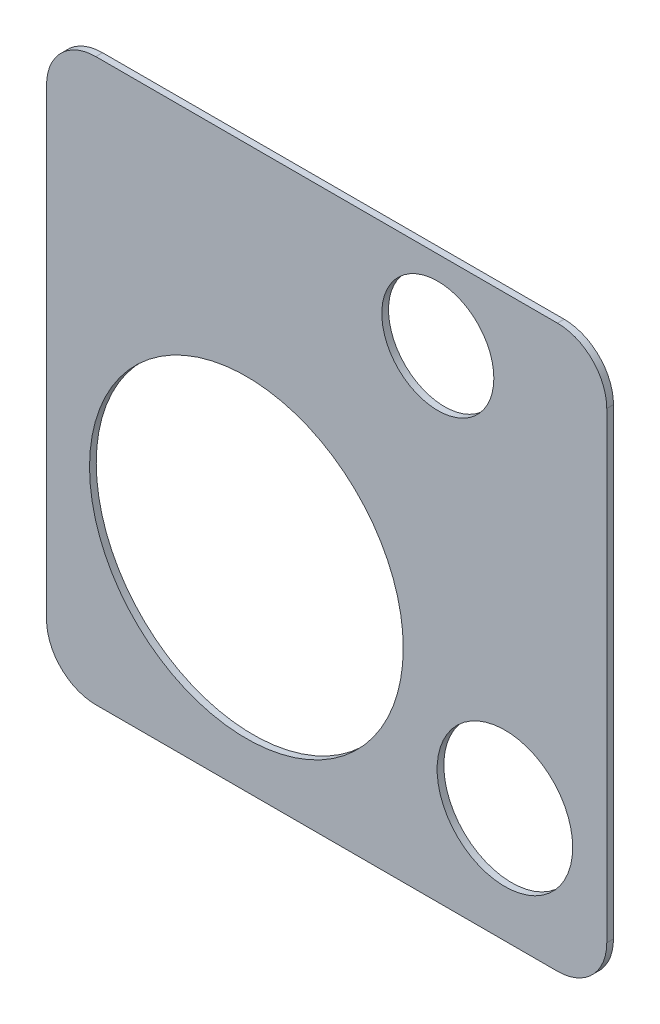
SolidWorks part; units mm, degrees
material "Pine"
ref_plane "Front Plane" through (0, 0, 0) normal (0, 0, 1) x (1, 0, 0)
ref_plane "Top Plane" through (0, 0, 0) normal (0, 1, 0) x (1, 0, 0)
ref_plane "Right Plane" through (0, 0, 0) normal (1, 0, 0) x (0, 0, -1)
sketch "Sketch1" plane through (0, 0, 0) normal (0, 0, 1) x (1, 0, 0)
  line L1 (0, 0) -> (500, 0)
  line L2 (0, 0) -> (0, 501)
  line L3 (0, 501) -> (500, 501)
  line L4 (500, 0) -> (500, 501)
  dimension "D1" = 500
  dimension "D2" = 501
extrude "Boss-Extrude1" add sketch "Sketch1" along normal blind 6
fillet "Fillet1" radius 44 4 edges at (0, 0, 3) (500, 0, 3) (0, 501, 3) (500, 501, 3)
sketch "Sketch2" plane through (0, 0, 6) normal (0, 0, 1) x (1, 0, 0)
  circle A0 centre (178.369, 181.0347) radius 156
  dimension "D1" = 312
sketch "Sketch3" plane through (0, 0, 6) normal (0, 0, 1) x (1, 0, 0)
  circle A1 centre (178.369, 181.0347) radius 140
  dimension "D1" = 280
extrude "Cut-Extrude2" cut sketch "Sketch3" against normal through all
sketch "Sketch4" plane through (0, 0, 6) normal (0, 0, 1) x (1, 0, 0)
  circle A0 centre (409.1034, 102.5162) radius 72.5
  dimension "D1" = 145
sketch "Sketch5" plane through (0, 0, 6) normal (0, 0, 1) x (1, 0, 0)
  circle A0 centre (409.1034, 102.5162) radius 60.5
  dimension "D1" = 121
extrude "Cut-Extrude3" cut sketch "Sketch5" against normal through all
sketch "Sketch6" plane through (0, 0, 6) normal (0, 0, 1) x (1, 0, 0)
  line L0 (500, 360) -> (0, 360)
  line L1 (500, 44) -> (500, 457) construction
  line L2 (0, 457) -> (0, 44) construction
  line L3 (44, 0) -> (456, 0) construction
  line L4 (456, 501) -> (44, 501) construction
  circle A0 centre (349.2286, 430) radius 50
  circle A1 centre (349.2286, 430) radius 50
  dimension "D1" = 100
  dimension "D3" = 100
  dimension "D2" = 360
  dimension "D4" = 71
extrude "Cut-Extrude5" cut sketch "Sketch6" against normal through all contours A1
sketch "Sketch7" plane through (0, 0, 6) normal (0, 0, 1) x (1, 0, 0)
  line L0 (0, 457) -> (0, 44) construction
  line L1 (456, 501) -> (44, 501) construction
  text T0 "ouisician" font "Century Gothic" height in points 72
  dimension "D1" = 80
  dimension "D2" = 80
sketch "Sketch10" plane through (0, 0, 6) normal (0, 0, 1) x (1, 0, 0)
  line L0 (0, 366) -> (500, 366)
  line L1 (0, 457) -> (0, 44) construction
  line L2 (500, 44) -> (500, 457) construction
  line L3 (456, 501) -> (44, 501) construction
  line L4 (0, 360) -> (500, 360)
  line L5 (44, 0) -> (456, 0) construction
  dimension "D1" = 500
  dimension "D2" = 135
  dimension "D3" = 360
